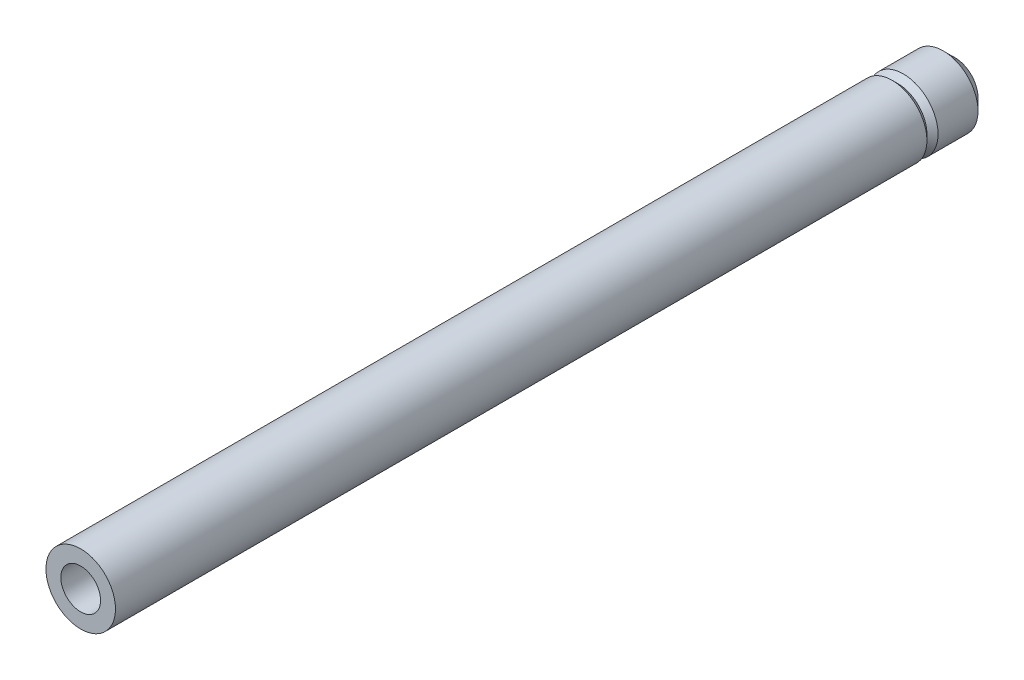
SolidWorks part; units mm, degrees
material "Al 6061-T6"
ref_plane "Front Plane" through (0, 0, 0) normal (0, 0, 1) x (1, 0, 0)
ref_plane "Top Plane" through (0, 0, 0) normal (0, 1, 0) x (1, 0, 0)
ref_plane "Right Plane" through (0, 0, 0) normal (1, 0, 0) x (0, 0, -1)
sketch "Sketch1" plane through (0, 0, 0) normal (1, 0, 0) x (0, 0, -1)
  line L0 (-90.1301, 0) -> (96.9397, 0) construction
  line L1 (-184.9764, 6.35) -> (91.8836, 6.35)
  line L2 (91.8836, 6.35) -> (91.8836, 6.858)
  line L3 (91.8836, 6.858) -> (94.4236, 6.858)
  line L4 (94.4236, 6.858) -> (94.4236, 7.366)
  line L5 (94.4236, 7.366) -> (90.6771, 11.1125)
  line L6 (90.6771, 11.1125) -> (77.9136, 11.1125)
  line L7 (77.9136, 11.1125) -> (76.1356, 9.3345)
  line L8 (76.1356, 9.3345) -> (74.3576, 11.1125)
  line L9 (74.3576, 11.1125) -> (-184.9764, 11.1125)
  line L10 (-184.9764, 11.1125) -> (-184.9764, 6.35)
  dimension "D1" = 45
  dimension "D2" = 45
  dimension "D3" = 279.4
  dimension "D4" = 2.54
  dimension "D5" = 6.35
  dimension "D6" = 6.858
  dimension "D7" = 7.366
  dimension "D8" = 11.1125
  dimension "D9" = 18.288
  dimension "D10" = 1.778
revolve "Revolve1" add sketch "Sketch1" angle 360 about L0
